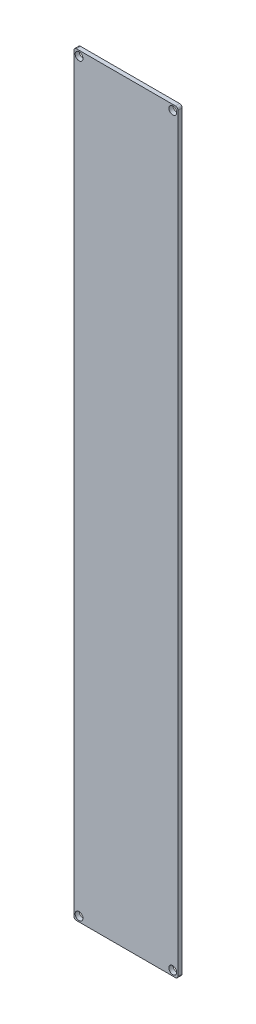
SolidWorks part; units mm, degrees
ref_plane "Front Plane" through (0, 0, 0) normal (0, 0, 1) x (1, 0, 0)
ref_plane "Top Plane" through (0, 0, 0) normal (0, 1, 0) x (1, 0, 0)
ref_plane "Right Plane" through (0, 0, 0) normal (1, 0, 0) x (0, 0, -1)
sketch "Sketch1" plane through (0, 0, 0) normal (0, 0, 1) x (1, 0, 0)
  line L1 (-35.5385, 79.3692) -> (4.4615, 79.3692)
  line L2 (-35.5385, 79.3692) -> (-35.5385, -210.6308)
  line L3 (-35.5385, -210.6308) -> (4.4615, -210.6308)
  line L4 (4.4615, 79.3692) -> (4.4615, -210.6308)
  dimension "D1" = 290
  dimension "D2" = 40
extrude "Boss-Extrude1" add sketch "Sketch1" along normal blind 1.6
sketch "Sketch2" plane through (0, 0, 1.6) normal (0, 0, 1) x (1, 0, 0)
  line L0 (-35.5385, 79.3692) -> (-35.5385, -210.6308) construction
  line L2 (4.4615, 79.3692) -> (-35.5385, 79.3692) construction
  line L3 (4.4615, -210.6308) -> (4.4615, 79.3692) construction
  line L4 (-35.5385, -210.6308) -> (4.4615, -210.6308) construction
  circle A0 centre (-33.5385, 77.3692) radius 1.5
  circle A1 centre (2.4615, 77.3692) radius 1.5
  circle A2 centre (-33.5385, -208.6308) radius 1.5
  circle A3 centre (2.4615, -208.6308) radius 1.5
  dimension "D1" = 3
  dimension "D2" = 3
  dimension "D3" = 3
  dimension "D4" = 3
  dimension "D5" = 2
  dimension "D6" = 2
  dimension "D7" = 2
  dimension "D8" = 2
  dimension "D9" = 2
  dimension "D10" = 2
  dimension "D11" = 2
  dimension "D12" = 2
extrude "Cut-Extrude1" cut sketch "Sketch2" against normal through all
fillet "Fillet1" radius 1 4 edges at (-35.5385, 79.3692, 0.8) (4.4615, 79.3692, 0.8) (4.4615, -210.6308, 0.8) (-35.5385, -210.6308, 0.8)
